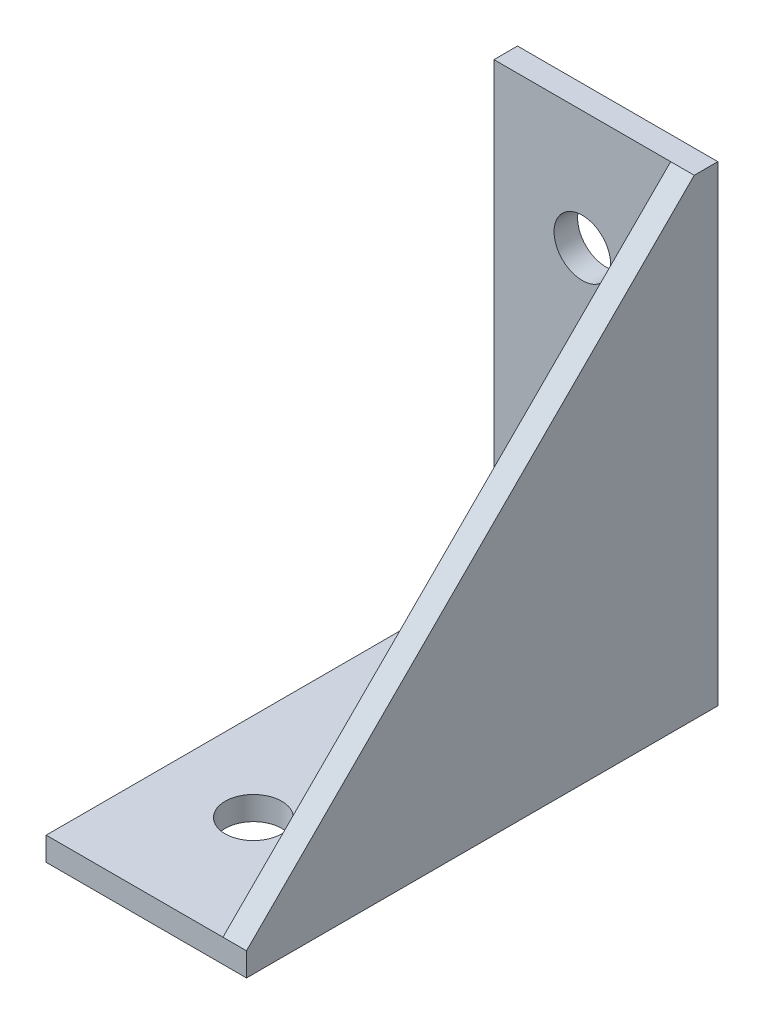
SolidWorks part; units mm, degrees
material "Alumina"
ref_plane "Front Plane" through (0, 0, 0) normal (0, 0, 1) x (1, 0, 0)
ref_plane "Top Plane" through (0, 0, 0) normal (0, 1, 0) x (1, 0, 0)
ref_plane "Right Plane" through (0, 0, 0) normal (1, 0, 0) x (0, 0, -1)
sketch "Sketch1" plane through (0, 0, 0) normal (1, 0, 0) x (0, 0, -1)
  line L0 (-38, 0) -> (0, 0)
  line L1 (0, 0) -> (0, 38)
  line L2 (0, 38) -> (-38, 0)
  dimension "D1" = 38
extrude "Boss-Extrude1" add sketch "Sketch1" along normal blind 2
sketch "Sketch2" plane through (2, 0, 0) normal (1, 0, 0) x (0, 0, -1)
  line L6 (0, 38) -> (2, 38)
  line L7 (-38, 0) -> (-38, -2)
  line L8 (-38, -2) -> (2, -2)
  line L9 (2, -2) -> (2, 38)
  line L10 (-38, -2) -> (2, -2)
  line L11 (2, -2) -> (2, 38)
  line L12 (0, 38) -> (0, 0)
  line L13 (0, 0) -> (-38, 0)
  dimension "D1" = 2
extrude "Boss-Extrude2" add sketch "Sketch2" against normal blind 17
sketch "Sketch3" plane through (0, 0, 0) normal (0, 1, 0) x (1, 0, 0)
  line L0 (-7.5, 0) -> (-7.5, -38) construction
  line L1 (-15, 0) -> (0, 0) construction
  line L2 (-15, -38) -> (0, -38) construction
  line L3 (-15, -19) -> (0, -19) construction
  line L4 (-15, 0) -> (-15, -38) construction
  line L5 (0, -38) -> (0, 0) construction
  line L6 (-15, 0) -> (0, 0) construction
  circle A0 centre (-7.5, -10.089) radius 2.1
  circle A1 centre (-7.5, -27.911) radius 2.1
  dimension "D1" = 4.2
revolve "Cut-Revolve1" cut sketch "Sketch3" angle 360 about L6
hole_wizard "M4 Clearance Hole1" positions "Sketch6" profile "Sketch7" hole size "M4" standard "ISO" end condition up to next
sketch "Sketch6" plane through (0, 0, 0) normal (0, 0, 1) x (1, 0, 0)
  point P0 (-7.5, 27.911)
  point P2 (-7.5, 10.089)
sketch "Sketch7" plane through (-7.5, 27.911, 0) normal (1, 0, 0) x (0, -1, 0)
  line L0 (0, 0) -> (0, 2)
  line L1 (0, 2) -> (2.4, 2)
  line L2 (2.4, 2) -> (2.4, 0)
  line L5 (2.4, 0) -> (0, 0)
  line L11 (0, -6.35) -> (0, 107.95) construction
  dimension "Thru Hole Dia." = 4.8
  dimension "Thru Hole Depth" = 2
hole_wizard "M4 Clearance Hole2" positions "Sketch8" profile "Sketch9" hole size "M4" standard "ISO" end condition up to next
sketch "Sketch8" plane through (0, 0, 0) normal (0, 1, 0) x (1, 0, 0)
  point P0 (-7.5, -10.089)
  point P2 (-7.5, -27.911)
sketch "Sketch9" plane through (-7.5, 0, 10.089) normal (1, 0, 0) x (0, 0, 1)
  line L0 (0, 0) -> (0, 2)
  line L1 (0, 2) -> (2.4, 2)
  line L2 (2.4, 2) -> (2.4, 0)
  line L5 (2.4, 0) -> (0, 0)
  line L11 (0, -6.35) -> (0, 107.95) construction
  dimension "Thru Hole Dia." = 4.8
  dimension "Thru Hole Depth" = 2
